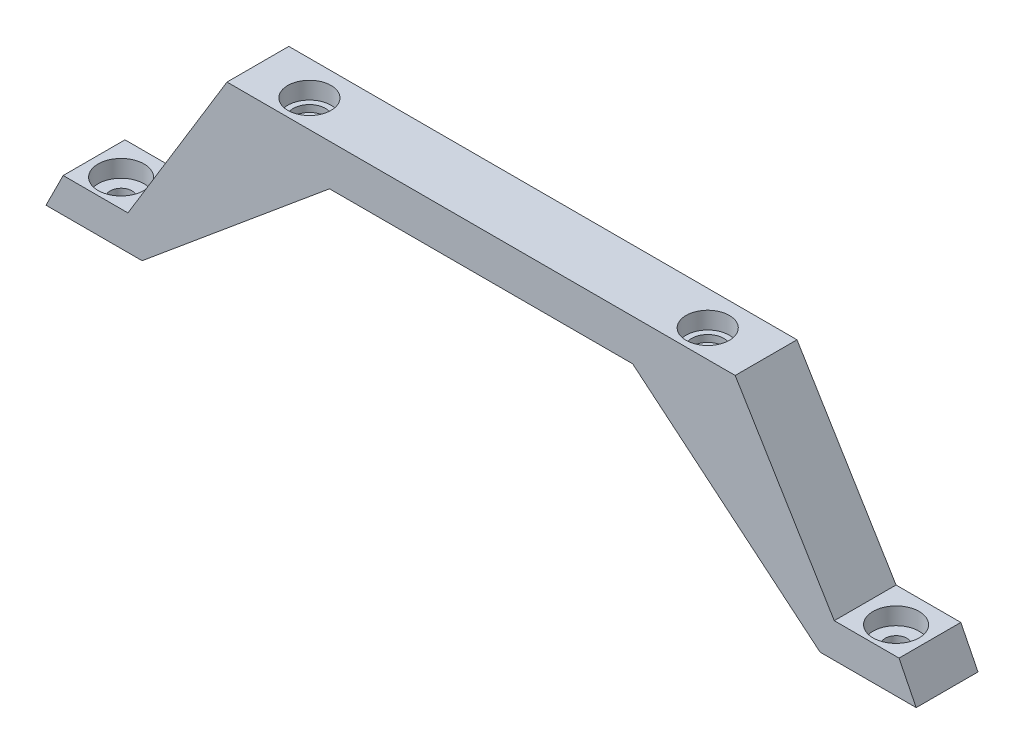
SolidWorks part; units mm, degrees
ref_plane "前视基准面" through (0, 0, 0) normal (0, 0, 1) x (1, 0, 0)
ref_plane "上视基准面" through (0, 0, 0) normal (0, 1, 0) x (1, 0, 0)
ref_plane "右视基准面" through (0, 0, 0) normal (1, 0, 0) x (0, 0, -1)
sketch "草图1" plane through (0, 0, 0) normal (0, 0, 1) x (1, 0, 0)
  line L0 (33.8113, 38.6957) -> (33.8113, 7.0528) construction
  line L1 (-3.1887, 13.0528) -> (33.8113, 13.0528)
  line L2 (-3.1887, 13.0528) -> (-17.6144, -10.6613)
  line L3 (-17.6144, -10.6613) -> (-25.0458, -10.6613)
  line L4 (33.8113, 13.0528) -> (33.8113, 7.0528)
  line L5 (15.602, 7.0528) -> (11.742, 7.0528)
  line L6 (11.742, 7.0528) -> (-15.5493, -15.6613)
  line L7 (33.8113, 7.0528) -> (15.602, 7.0528)
  line L8 (-25.0458, -10.6613) -> (-27.0458, -10.6613)
  line L9 (-27.0458, -10.6613) -> (-29.5458, -15.6613)
  line L10 (-29.5458, -15.6613) -> (-27.5458, -15.6613)
  line L13 (-15.5493, -15.6613) -> (-23.6887, -15.6613)
  line L20 (-27.5458, -15.6613) -> (-23.6887, -15.6613)
  point P0 (33.8113, 10.0528)
  point P7 (-17.6144, -10.6613)
  point P10 (-16.1887, -12.9472)
  point P11 (-17.5487, -15.6613)
  dimension "D2" = 5
extrude "凸台-拉伸1" add sketch "草图1" along normal blind 10
ref_plane "基准面3" through (33.8113, 0, 0) normal (1, 0, 0) x (0, 0, -1)
mirror "镜向1" about plane through (33.8113, 13.0528, 10) normal (-1, 0, 0) of "凸台-拉伸1"
ref_plane "基准面1" through (0, 0, 5) normal (0, 0, 1) x (1, 0, 0)
sketch "草图5" plane through (0, 0, 5) normal (0, 0, 1) x (1, 0, 0)
  line L0 (33.8113, 20.2752) -> (33.8113, -16.9928) construction
  line L1 (70.8113, 13.0528) -> (-3.1887, 13.0528) construction
  line L2 (7.9613, 13.0528) -> (7.9613, 10.5528)
  line L3 (7.9613, 10.5528) -> (7.1613, 10.5528)
  line L4 (7.1613, 10.5528) -> (7.1613, 9.5528)
  line L5 (7.1613, 9.5528) -> (6.3613, 9.5528)
  line L6 (4.8113, 13.0528) -> (4.8113, 2.5746) construction
  line L7 (4.8113, 13.0528) -> (7.9613, 13.0528)
  line L8 (6.3613, 9.5528) -> (4.8113, 9.5528)
  line L9 (4.8113, 9.5528) -> (4.8113, 13.0528)
  point P2 (4.8113, 13.0528)
  point P3 (62.8113, 13.0274)
  point P6 (7.9613, 13.0528)
  point P13 (6.3613, 9.5528)
  dimension "D2" = 29
  dimension "D3" = 3.15
revolve "切除-旋转7" cut sketch "草图5" angle 360 about L9
sketch "草图7" plane through (0, 9.5528, 0) normal (0, 1, 0) x (1, 0, 0)
  circle A0 centre (4.8113, -5) radius 1.55
  dimension "D1" = 3.1
extrude "切除-拉伸1" cut sketch "草图7" against normal through all
ref_plane "基准面2" through (0, -1.9472, 0) normal (0, 1, 0) x (1, 0, 0)
sketch "草图8" plane through (0, -1.9472, 0) normal (0, 1, 0) x (1, 0, 0)
  line L1 (8.3331, -5) -> (6.5722, -1.95)
  line L2 (6.5722, -1.95) -> (3.0504, -1.95)
  line L3 (3.0504, -1.95) -> (1.2895, -5)
  line L4 (1.2895, -5) -> (3.0504, -8.05)
  line L5 (3.0504, -8.05) -> (6.5722, -8.05)
  line L6 (6.5722, -8.05) -> (8.3331, -5)
  circle A0 centre (4.8113, -5) radius 3.05 construction
  dimension "D1" = 6.1
extrude "切除-拉伸2" cut sketch "草图8" along normal blind 8.5
sketch "草图10" plane through (0, -10.6613, 0) normal (0, 1, 0) x (1, 0, 0)
  line L0 (-17.6144, -10) -> (-27.0458, -10) construction
  line L3 (-17.6144, -10) -> (-17.6144, 0) construction
  circle A1 centre (-22.6144, -5) radius 1.575
  dimension "D1" = 3.15
  dimension "D4" = 5
  dimension "D3" = 5
extrude "切除-拉伸4" cut sketch "草图10" against normal blind 12
sketch "草图11" plane through (0, -10.6613, 0) normal (0, 1, 0) x (1, 0, 0)
  circle A0 centre (-22.6144, -5) radius 3.35
  dimension "D1" = 6.7
extrude "切除-拉伸5" cut sketch "草图11" against normal blind 2.5
mirror "镜向2" about plane through (33.8113, 0, 0) normal (1, 0, 0) of "切除-旋转7", "切除-拉伸1", "切除-拉伸2", "切除-拉伸4", "切除-拉伸5"
sketch "草图12" plane through (0, 13.0528, 0) normal (0, 1, 0) x (1, 0, 0)
  line L0 (-29.5458, -9) -> (97.1684, -9)
  line L1 (-29.5458, -10) -> (-29.5458, 0) construction
  line L2 (97.1684, -10) -> (97.1684, 0) construction
  line L3 (97.1684, -9) -> (97.1684, -10)
  line L4 (94.6684, -10) -> (97.1684, -10) construction
  line L5 (97.1684, -10) -> (-29.5458, -10)
  line L6 (-29.5458, -10) -> (-29.5458, -9)
  dimension "D1" = 1
extrude "切除-拉伸6" cut sketch "草图12" against normal through all
